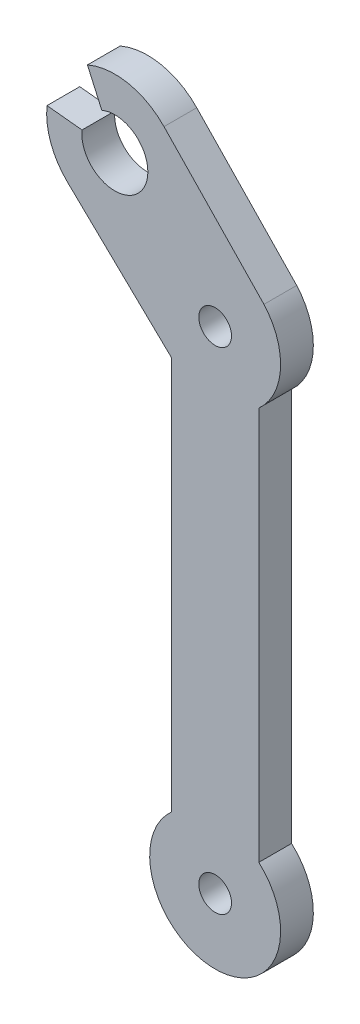
SolidWorks part; units mm, degrees
ref_plane "Plan de face" through (0, 0, 0) normal (0, 0, 1) x (1, 0, 0)
ref_plane "Plan de dessus" through (0, 0, 0) normal (0, 1, 0) x (1, 0, 0)
ref_plane "Plan de droite" through (0, 0, 0) normal (1, 0, 0) x (0, 0, -1)
sketch "Esquisse1" plane through (0, 0, 0) normal (0, 0, 1) x (1, 0, 0)
  line L0 (-10.4388, -0.1126) -> (-10.4388, 20.284)
  line L1 (-10.4388, -0.1126) -> (-10.4388, -15.7718)
  line L2 (-6.4388, 24.7561) -> (-6.4388, -20.2439) construction
  line L3 (-2.4388, -15.7718) -> (-2.4388, 20.284)
  line L4 (-15.5448, 33.8622) -> (-19.5128, 42.7335)
  line L5 (-6.4388, 24.7561) -> (-40.6659, 58.9832) construction
  line L6 (-15.6311, 33.9485) -> (-28.1096, 35.2384)
  line L7 (-10.4388, 20.284) -> (-19.9634, 29.4436)
  line L9 (-1.9666, 28.7561) -> (-11.1262, 38.2807)
  line L10 (-19.9634, 29.4436) -> (-11.1262, 38.2807) construction
  line L11 (-15.5448, 33.8622) -> (-15.6311, 33.9485)
  arc A0 (-2.4388, 20.284) -> (-2.2671, 29.0686) centre (-6.4388, 24.7561) ccw
  circle A1 centre (-6.4388, 24.7561) radius 1.5
  arc A2 (-10.4388, -15.7718) -> (-2.4388, -15.7718) centre (-6.4388, -20.2439) ccw
  circle A3 centre (-6.4388, -20.2439) radius 1.5
  circle A4 centre (-15.6311, 33.9485) radius 3.025
  arc A5 (-11.1262, 38.2807) -> (-19.9634, 29.4436) centre (-15.6311, 33.9485) ccw
  arc A6 (-10.7513, 20.5845) -> (-10.4388, 20.284) centre (-6.4388, 24.7561) ccw
  point P1 (-18.8335, 43.0764)
  dimension "D3" = 60
  dimension "D5" = 12
  dimension "D6" = 3
  dimension "D2" = 6.05
  dimension "D7" = 12.5
  dimension "D1" = 135
extrude "Boss.-Extru.1" add sketch "Esquisse1" along normal blind 3 contours L9 A5 L7 L0 L1 A2 L3 A0 A1 A3 A4
